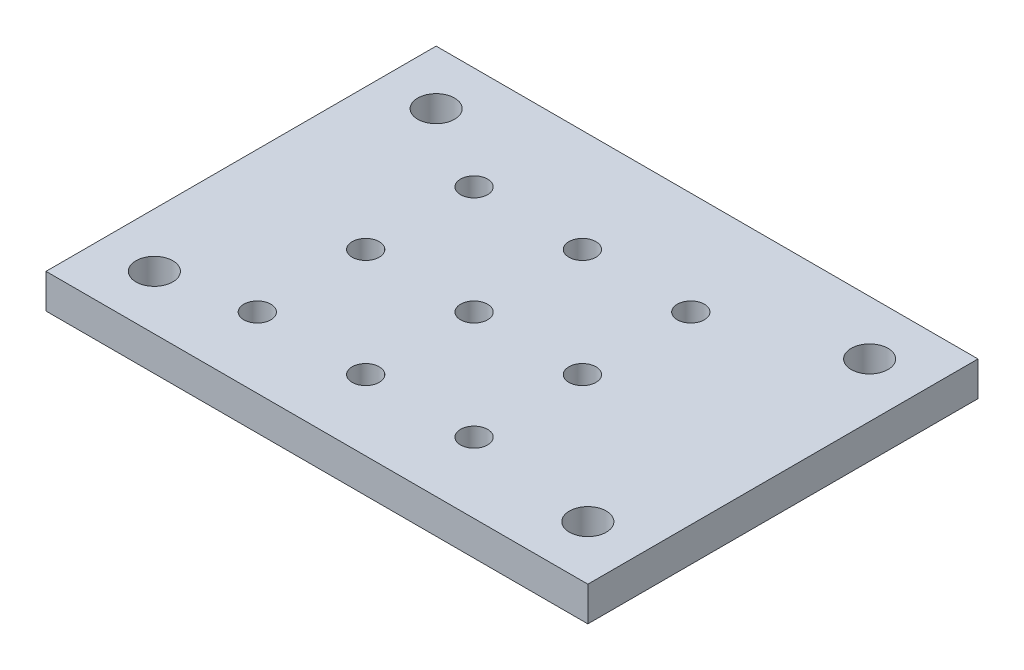
SolidWorks part; units mm, degrees
ref_plane "Front Plane" through (0, 0, 0) normal (0, 0, 1) x (1, 0, 0)
ref_plane "Top Plane" through (0, 0, 0) normal (0, 1, 0) x (1, 0, 0)
ref_plane "Right Plane" through (0, 0, 0) normal (1, 0, 0) x (0, 0, -1)
sketch "Sketch1" plane through (0, 0, 0) normal (0, 1, 0) x (1, 0, 0)
  line L0 (45, 31) -> (5, 31) construction
  line L1 (0, 0) -> (50, 0)
  line L2 (0, 0) -> (0, 36)
  line L3 (0, 36) -> (50, 36)
  line L4 (50, 0) -> (50, 36)
  line L6 (45, 31) -> (45, 5) construction
  circle A19 centre (13, 6.5) radius 1.25
  circle A28 centre (5, 5) radius 1.7
  circle A29 centre (5, 31) radius 1.7
  circle A30 centre (45, 31) radius 1.7
  circle A31 centre (45, 5) radius 1.7
  circle A32 centre (23, 6.5) radius 1.25
  circle A33 centre (33, 6.5) radius 1.25
  circle A34 centre (23, 16.5) radius 1.25
  circle A35 centre (33, 16.5) radius 1.25
  circle A36 centre (23, 26.5) radius 1.25
  circle A37 centre (33, 26.5) radius 1.25
  circle A38 centre (13, 16.5) radius 1.25
  circle A39 centre (13, 26.5) radius 1.25
  point P7 (45, 18)
  point P9 (25, 31)
  point P10 (25, 36)
  point P20 (50, 18)
  dimension "D5" = 40
  dimension "D6" = 26
  dimension "D3" = 2.5
  dimension "D8" = 3.4
  dimension "D1" = 50
  dimension "D2" = 36
  dimension "D4" = 8
  dimension "D7" = 1.5
  dimension "D9" = 3
extrude "Boss-Extrude1" add sketch "Sketch1" along normal blind 3.175
equation "\"o\"= 10mm"
equation "\"P\"= 10"
